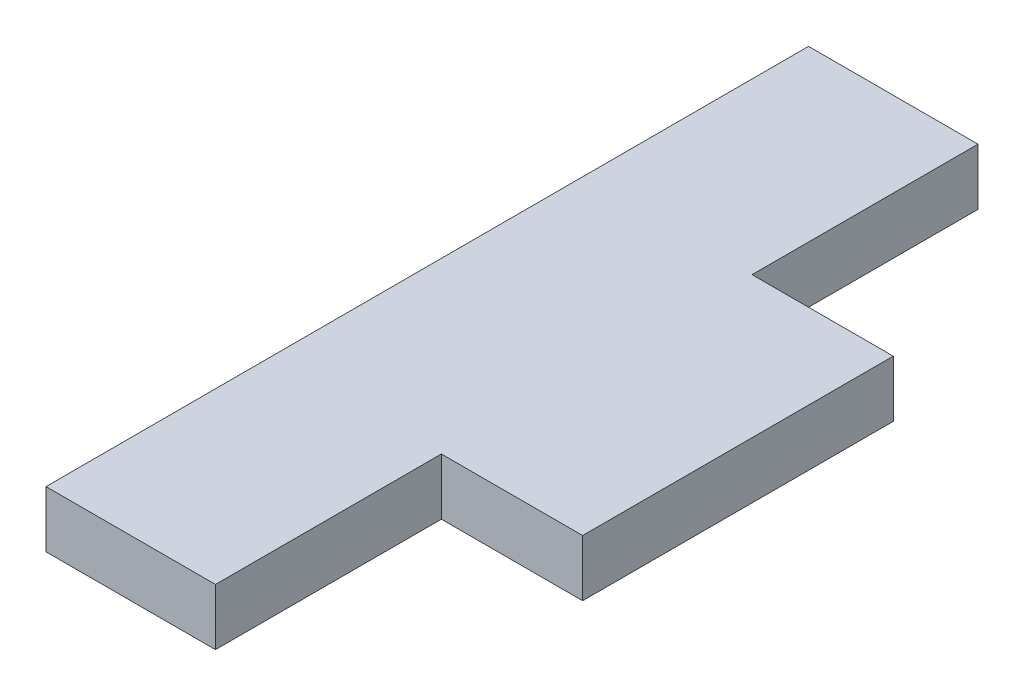
SolidWorks part; units mm, degrees
ref_plane "Front Plane" through (0, 0, 0) normal (0, 0, 1) x (1, 0, 0)
ref_plane "Top Plane" through (0, 0, 0) normal (0, 1, 0) x (1, 0, 0)
ref_plane "Right Plane" through (0, 0, 0) normal (1, 0, 0) x (0, 0, -1)
sketch "Sketch1" plane through (0, 0, 0) normal (0, 1, 0) x (1, 0, 0)
  line L0 (4.5471, 64.0065) -> (4.5471, 24.0065)
  line L1 (4.5471, -70.9935) -> (-25.4529, -70.9935)
  line L3 (4.5471, 64.0065) -> (-25.4529, 64.0065)
  line L4 (-25.4529, -70.9935) -> (-25.4529, 64.0065)
  line L5 (4.5471, 24.0065) -> (29.5471, 24.0065)
  line L7 (4.5471, -30.9935) -> (29.5471, -30.9935)
  line L8 (29.5471, 24.0065) -> (29.5471, -30.9935)
  line L9 (4.5471, -30.9935) -> (4.5471, -70.9935)
  point P0 (0, 0)
  point P6 (20.4621, 1.622)
  dimension "D1" = 135
  dimension "D2" = 30
  dimension "D3" = 30
  dimension "D4" = 55
  dimension "D5" = 25
  dimension "D6" = 40
extrude "Boss-Extrude1" add sketch "Sketch1" along normal blind 10
